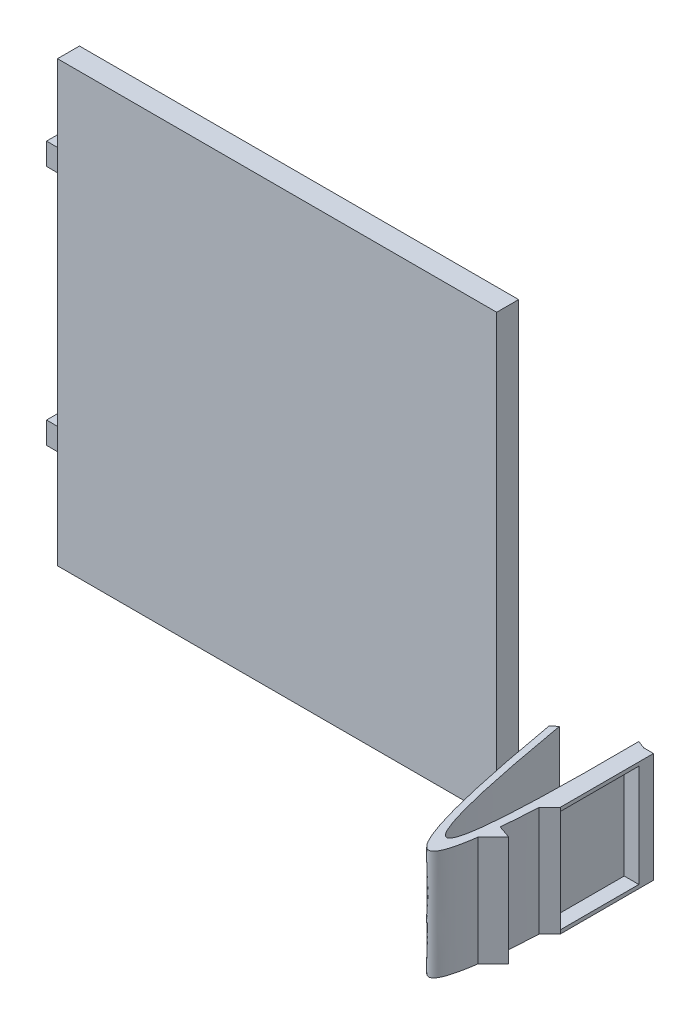
SolidWorks part; units mm, degrees
ref_plane "Face" through (0, 0, 0) normal (0, 0, 1) x (1, 0, 0)
ref_plane "Dessus" through (0, 0, 0) normal (0, 1, 0) x (1, 0, 0)
ref_plane "Droite" through (0, 0, 0) normal (1, 0, 0) x (0, 0, -1)
sketch "Esquisse2" plane through (0, 0, 0) normal (0, 0, 1) x (1, 0, 0)
  line L0 (-62.5291, 26.9529) -> (-179.9646, 26.9529) construction
  line L1 (-122.5291, 56.9529) -> (-62.5291, 56.9529)
  line L2 (-122.5291, 56.9529) -> (-122.5291, -3.0471)
  line L3 (-122.5291, -3.0471) -> (-62.5291, -3.0471)
  line L4 (-62.5291, 56.9529) -> (-62.5291, -3.0471)
  dimension "D1" = 60
  dimension "D2" = 60
extrude "Boss.-Extru.5" add sketch "Esquisse2" along normal blind 3
sketch "Esquisse4" plane through (0, 0, 0) normal (0, 0, 1) x (1, 0, 0)
  line L0 (-122.5291, 56.9529) -> (-122.5291, -3.0471) construction
  line L1 (-122.5291, 41.9529) -> (-125.5291, 41.9529)
  line L2 (-122.5291, 41.9529) -> (-122.5291, 44.9529)
  line L3 (-122.5291, 44.9529) -> (-125.5291, 44.9529)
  line L4 (-125.5291, 41.9529) -> (-125.5291, 44.9529)
  line L5 (-62.5291, 26.9529) -> (-182.2707, 26.9529) construction
  line L6 (-122.5291, 8.9529) -> (-125.5291, 8.9529)
  line L7 (-122.5291, 8.9529) -> (-122.5291, 11.9529)
  line L8 (-122.5291, 11.9529) -> (-125.5291, 11.9529)
  line L9 (-125.5291, 8.9529) -> (-125.5291, 11.9529)
  line L10 (-62.5291, -3.0471) -> (-62.5291, 56.9529) construction
  dimension "D1" = 12
  dimension "D2" = 12
  dimension "D3" = 3
  dimension "D4" = 3
extrude "Boss.-Extru.6" add sketch "Esquisse4" along normal blind 1.5
sketch "Esquisse5" plane through (0, 0, 0) normal (0, 1, 0) x (1, 0, 0)
  line L0 (-43.6556, -24.3989) -> (-41.5704, -22.3137)
  line L1 (-41.5704, -22.3137) -> (-43.3482, -21.7007)
  line L2 (-43.0115, -16.7145) -> (-41.5704, -15.2734)
  line L3 (-41.5704, -15.2734) -> (-41.5704, -2.5379)
  line L4 (-41.5704, -2.5379) -> (-42.893, -2.5379)
  line L5 (-43.3482, -21.7007) -> (-41.5704, -22.3137)
  line L6 (-51.9661, -6.3709) -> (-51.1963, -5.7789)
  line L7 (-43.9884, -2.1282) -> (-42.893, -2.5379)
  spline S0 degree 3 poles (-51.9661, -6.3709) (-43.9064, -52.1609) (-42.4311, -17.9236) (-42.893, -2.5379) knots 0 0 0 0 1 1 1 1
  spline S1 degree 2 poles (-51.1963, -5.7789) (-43.616, -49.183) (-43.9884, -2.1282) knots 0 0 0 1 1 1
extrude "Boss.-Extru.7" add sketch "Esquisse5" along normal blind 15 separate body contours S1 L6 S0 L7 | S0 L0 L1 | S0 L2 L3 L4
sketch "Esquisse6" plane through (-41.5704, 0, 0) normal (1, 0, 0) x (0, 0, -1)
  line L10 (-15.2734, 15) -> (-15.2734, 0) construction
  line L11 (-15.2734, 0.5) -> (-4.5379, 0.5)
  line L12 (-15.2734, 0.5) -> (-15.2734, 14.5)
  line L13 (-15.2734, 14.5) -> (-4.5379, 14.5)
  line L14 (-4.5379, 0.5) -> (-4.5379, 14.5)
  line L15 (-2.5379, 15) -> (-2.5379, 0) construction
  dimension "D1" = 2
  dimension "D2" = 0.5
  dimension "D3" = 0.5
extrude "Enlèv. mat.-Extru.3" cut sketch "Esquisse6" against normal blind 2
equation "\"1.5.00mm\"=3"
